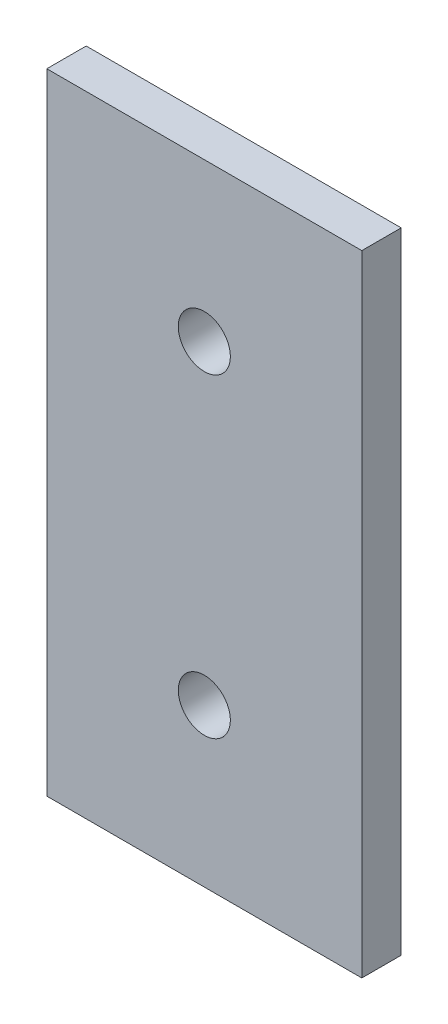
SolidWorks part; units mm, degrees
ref_plane "Front Plane" through (0, 0, 0) normal (0, 0, 1) x (1, 0, 0)
ref_plane "Top Plane" through (0, 0, 0) normal (0, 1, 0) x (1, 0, 0)
ref_plane "Right Plane" through (0, 0, 0) normal (1, 0, 0) x (0, 0, -1)
sketch "Sketch1" plane through (0, 0, 0) normal (0, 0, 1) x (1, 0, 0)
  line L1 (-12.7, -25.4) -> (12.7, -25.4)
  line L2 (-12.7, -25.4) -> (-12.7, 25.4)
  line L3 (-12.7, 25.4) -> (12.7, 25.4)
  line L4 (12.7, -25.4) -> (12.7, 25.4)
  line L5 (-12.7, -25.4) -> (12.7, 25.4) construction
  line L6 (-12.7, 25.4) -> (12.7, -25.4) construction
  circle A0 centre (0, 12.7) radius 2.1
  circle A1 centre (0, -12.7) radius 2.1
  point P0 (0, 0)
  dimension "D5" = 4.2
  dimension "D6" = 4.2
  dimension "D1" = 25.4
  dimension "D2" = 50.8
  dimension "D3" = 12.7
  dimension "D4" = 12.7
extrude "Boss-Extrude1" add sketch "Sketch1" along normal blind 3.175
